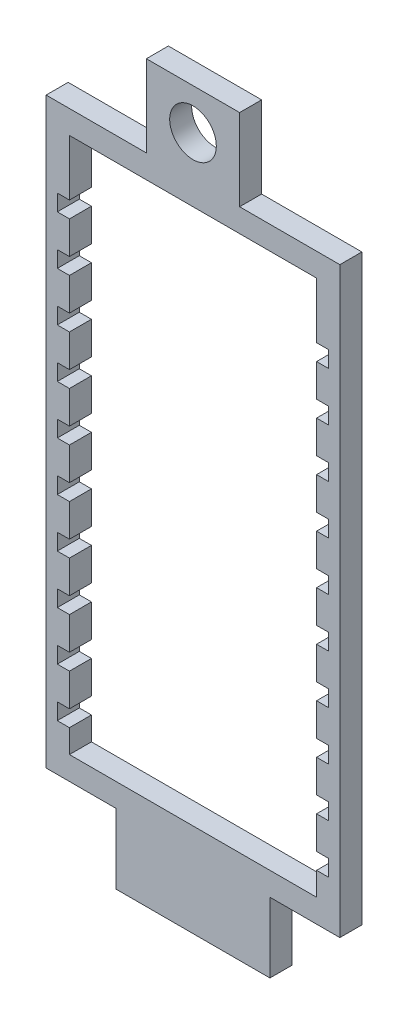
SolidWorks part; units mm, degrees
ref_plane "Front Plane" through (0, 0, 0) normal (0, 0, 1) x (1, 0, 0)
ref_plane "Top Plane" through (0, 0, 0) normal (0, 1, 0) x (1, 0, 0)
ref_plane "Right Plane" through (0, 0, 0) normal (1, 0, 0) x (0, 0, -1)
sketch "Sketch1" plane through (0, 0, 0) normal (0, 0, 1) x (1, 0, 0)
  line L0 (40.005, 171.45) -> (40.005, 0) construction
  line L2 (0, 19.05) -> (0, 177.8)
  line L3 (0, 177.8) -> (6.35, 177.8)
  line L4 (6.35, 25.4) -> (6.35, 171.45)
  line L5 (6.35, 177.8) -> (73.66, 177.8)
  line L7 (6.35, 171.45) -> (73.66, 171.45)
  line L9 (80.01, 177.8) -> (73.66, 177.8)
  line L10 (73.66, 25.4) -> (73.66, 171.45)
  line L12 (80.01, 19.05) -> (80.01, 177.8)
  line L13 (6.35, 88.9) -> (73.66, 88.9) construction
  line L16 (19.05, 0) -> (60.96, 0)
  line L17 (19.05, 19.05) -> (19.05, 0)
  line L18 (19.05, 19.05) -> (0, 19.05)
  line L19 (6.35, 25.4) -> (73.66, 25.4)
  line L20 (60.96, 19.05) -> (60.96, 0)
  line L23 (60.96, 19.05) -> (80.01, 19.05)
  point P22 (40.005, 25.4)
  dimension "D1" = 177.8
  dimension "D2" = 19.05
  dimension "D3" = 6.35
  dimension "D4" = 67.31
  dimension "D5" = 67.31
  dimension "D6" = 6.35
  dimension "D7" = 19.05
extrude "Boss-Extrude1" add sketch "Sketch1" against normal blind 5.9944
sketch "Sketch2" plane through (0, 0, 0) normal (0, 0, 1) x (1, 0, 0)
  line L0 (6.35, 171.45) -> (6.35, 25.4) construction
  line L1 (3.048, 31.75) -> (9.652, 31.75)
  line L2 (3.048, 31.75) -> (3.048, 36.195)
  line L3 (3.048, 36.195) -> (9.652, 36.195)
  line L4 (9.652, 31.75) -> (9.652, 36.195)
  line L5 (3.048, 31.75) -> (9.652, 36.195) construction
  line L6 (3.048, 36.195) -> (9.652, 31.75) construction
  line L7 (40.005, 171.45) -> (40.005, 25.4) construction
  line L8 (3.048, 45.085) -> (3.048, 49.53)
  line L9 (19.05, 0) -> (60.96, 0) construction
  line L10 (73.66, 171.45) -> (6.35, 171.45) construction
  line L71 (3.048, 45.085) -> (9.652, 45.085)
  line L72 (9.652, 45.085) -> (9.652, 49.53)
  line L73 (3.048, 49.53) -> (9.652, 49.53)
  line L78 (3.048, 58.42) -> (3.048, 62.865)
  line L79 (3.048, 58.42) -> (9.652, 58.42)
  line L80 (9.652, 58.42) -> (9.652, 62.865)
  line L81 (3.048, 62.865) -> (9.652, 62.865)
  line L86 (3.048, 71.755) -> (3.048, 76.2)
  line L87 (3.048, 71.755) -> (9.652, 71.755)
  line L88 (9.652, 71.755) -> (9.652, 76.2)
  line L89 (3.048, 76.2) -> (9.652, 76.2)
  line L94 (3.048, 85.09) -> (3.048, 89.535)
  line L95 (3.048, 85.09) -> (9.652, 85.09)
  line L96 (9.652, 85.09) -> (9.652, 89.535)
  line L97 (3.048, 89.535) -> (9.652, 89.535)
  line L102 (3.048, 98.425) -> (3.048, 102.87)
  line L103 (3.048, 98.425) -> (9.652, 98.425)
  line L104 (9.652, 98.425) -> (9.652, 102.87)
  line L105 (3.048, 102.87) -> (9.652, 102.87)
  line L110 (3.048, 111.76) -> (3.048, 116.205)
  line L111 (3.048, 111.76) -> (9.652, 111.76)
  line L112 (9.652, 111.76) -> (9.652, 116.205)
  line L113 (3.048, 116.205) -> (9.652, 116.205)
  line L118 (3.048, 125.095) -> (3.048, 129.54)
  line L119 (3.048, 125.095) -> (9.652, 125.095)
  line L120 (9.652, 125.095) -> (9.652, 129.54)
  line L121 (3.048, 129.54) -> (9.652, 129.54)
  line L126 (3.048, 138.43) -> (3.048, 142.875)
  line L127 (3.048, 138.43) -> (9.652, 138.43)
  line L128 (9.652, 138.43) -> (9.652, 142.875)
  line L129 (3.048, 142.875) -> (9.652, 142.875)
  line L134 (3.048, 151.765) -> (3.048, 156.21)
  line L135 (3.048, 151.765) -> (9.652, 151.765)
  line L136 (9.652, 151.765) -> (9.652, 156.21)
  line L137 (3.048, 156.21) -> (9.652, 156.21)
  line L142 (6.35, 25.4) -> (73.66, 25.4) construction
  line L143 (76.962, 36.195) -> (70.358, 31.75) construction
  line L144 (76.962, 31.75) -> (70.358, 36.195) construction
  line L145 (76.962, 156.21) -> (70.358, 156.21)
  line L146 (70.358, 151.765) -> (70.358, 156.21)
  line L147 (76.962, 151.765) -> (70.358, 151.765)
  line L148 (76.962, 151.765) -> (76.962, 156.21)
  line L149 (76.962, 142.875) -> (70.358, 142.875)
  line L150 (70.358, 138.43) -> (70.358, 142.875)
  line L151 (76.962, 138.43) -> (70.358, 138.43)
  line L152 (76.962, 138.43) -> (76.962, 142.875)
  line L153 (76.962, 129.54) -> (70.358, 129.54)
  line L154 (70.358, 125.095) -> (70.358, 129.54)
  line L155 (76.962, 125.095) -> (70.358, 125.095)
  line L156 (76.962, 125.095) -> (76.962, 129.54)
  line L157 (76.962, 116.205) -> (70.358, 116.205)
  line L158 (70.358, 111.76) -> (70.358, 116.205)
  line L159 (76.962, 111.76) -> (70.358, 111.76)
  line L160 (76.962, 111.76) -> (76.962, 116.205)
  line L161 (76.962, 102.87) -> (70.358, 102.87)
  line L162 (70.358, 98.425) -> (70.358, 102.87)
  line L163 (76.962, 98.425) -> (70.358, 98.425)
  line L164 (76.962, 98.425) -> (76.962, 102.87)
  line L165 (76.962, 89.535) -> (70.358, 89.535)
  line L166 (70.358, 85.09) -> (70.358, 89.535)
  line L167 (76.962, 85.09) -> (70.358, 85.09)
  line L168 (76.962, 85.09) -> (76.962, 89.535)
  line L169 (76.962, 76.2) -> (70.358, 76.2)
  line L170 (70.358, 71.755) -> (70.358, 76.2)
  line L171 (76.962, 71.755) -> (70.358, 71.755)
  line L172 (76.962, 71.755) -> (76.962, 76.2)
  line L173 (76.962, 62.865) -> (70.358, 62.865)
  line L174 (70.358, 58.42) -> (70.358, 62.865)
  line L175 (76.962, 58.42) -> (70.358, 58.42)
  line L176 (76.962, 58.42) -> (76.962, 62.865)
  line L177 (76.962, 49.53) -> (70.358, 49.53)
  line L178 (70.358, 45.085) -> (70.358, 49.53)
  line L179 (76.962, 45.085) -> (70.358, 45.085)
  line L180 (76.962, 45.085) -> (76.962, 49.53)
  line L181 (70.358, 31.75) -> (70.358, 36.195)
  line L182 (76.962, 36.195) -> (70.358, 36.195)
  line L183 (76.962, 31.75) -> (76.962, 36.195)
  line L184 (76.962, 31.75) -> (70.358, 31.75)
  point P0 (6.35, 33.9725)
  point P91 (73.66, 33.9725)
  dimension "D1" = 6.604
  dimension "D2" = 10
  dimension "D3" = 31.75
  dimension "D4" = 4.445
extrude "Cut-Extrude1" cut sketch "Sketch2" against normal through all
sketch "Sketch3" plane through (0, 0, 0) normal (0, 0, 1) x (1, 0, 0)
  line L0 (40.005, 177.8) -> (40.005, 200.025) construction
  line L1 (80.01, 177.8) -> (0, 177.8) construction
  line L2 (27.305, 177.8) -> (27.305, 200.025)
  line L3 (27.305, 200.025) -> (52.705, 200.025)
  line L4 (52.705, 177.8) -> (52.705, 200.025)
  line L5 (27.305, 177.8) -> (52.705, 177.8)
  circle A0 centre (40.005, 188.9125) radius 6.35
  point P9 (40.005, 200.025)
  point P11 (40.005, 200.025)
  dimension "D1" = 22.225
  dimension "D2" = 12.7
extrude "Boss-Extrude2" add sketch "Sketch3" along direction (0, 0, 1) on the side against the normal up to surface (5.9944 mm away)
